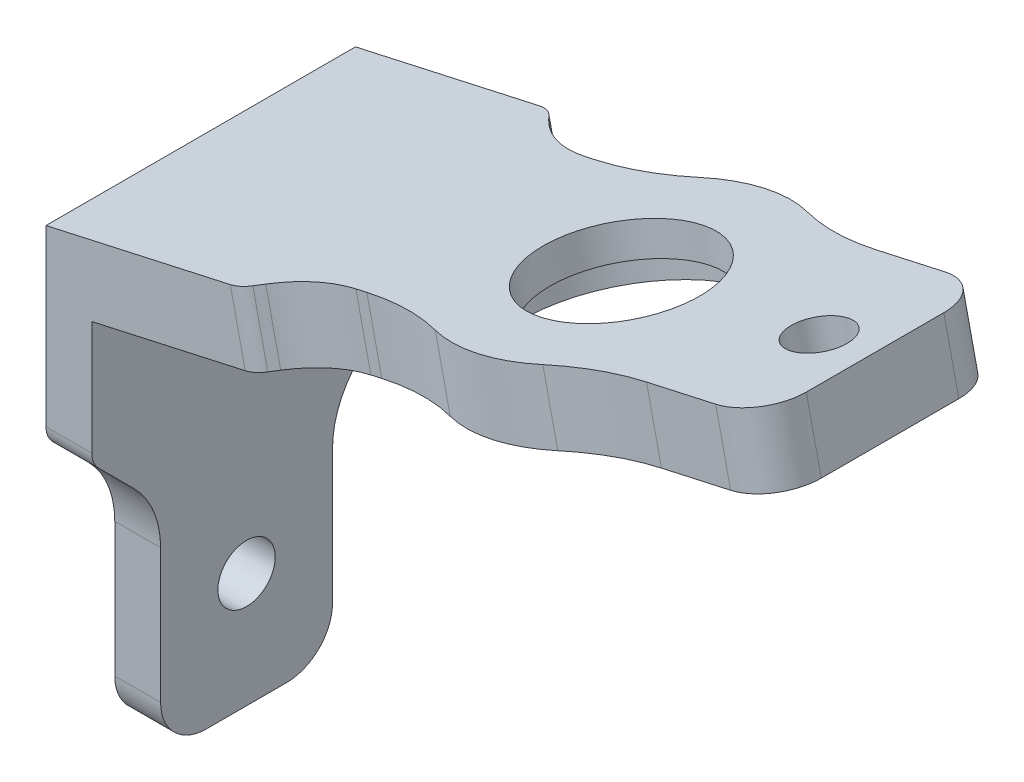
SolidWorks part; units mm, degrees
material "ABS"
ref_plane "Front Plane" through (0, 0, 0) normal (0, 0, 1) x (1, 0, 0)
ref_plane "Top Plane" through (0, 0, 0) normal (0, 1, 0) x (1, 0, 0)
ref_plane "Right Plane" through (0, 0, 0) normal (1, 0, 0) x (0, 0, -1)
sketch "Sketch2" plane through (-8.2998, 37.3265, 0) normal (-0.2171, 0.9762, 0) x (0.9762, 0.2171, 0)
  line L0 (-4.143, -6.75) -> (-4.143, 6.75) construction
  line L1 (-4.143, 6.75) -> (-8.9127, 6.75) construction
  line L2 (-8.9127, 6.75) -> (-8.9127, -6.75) construction
  line L3 (-8.9127, -6.75) -> (-4.143, -6.75) construction
  line L4 (-3.643, -6.75) -> (-2.0572, -6.75) construction
  line L5 (-1.3501, -6.4571) -> (-1.0646, -6.1716) construction
  line L6 (1.7639, -5) -> (14.3434, -5) construction
  line L7 (14.3434, -5) -> (14.3434, 5) construction
  line L8 (14.3434, 5) -> (1.7639, 5) construction
  line L9 (-1.0646, 6.1716) -> (-1.3501, 6.4571) construction
  line L10 (-2.0572, 6.75) -> (-3.643, 6.75) construction
  line L11 (-3.643, 6.75) -> (-3.643, -6.75) construction
  line L12 (19.8434, -3) -> (19.8434, 3) construction
  line L13 (17.8434, 5) -> (14.8434, 5) construction
  line L14 (14.8434, 5) -> (14.8434, -5) construction
  line L15 (14.8434, -5) -> (17.8434, -5) construction
  line L16 (-4.143, -6.75) -> (-4.143, 6.75) construction
  line L17 (-4.143, 6.75) -> (-8.9127, 6.75)
  line L18 (-8.9127, 6.75) -> (-8.9127, -6.75)
  line L19 (-8.9127, -6.75) -> (-4.143, -6.75)
  line L20 (-3.643, -6.75) -> (-2.0572, -6.75)
  line L21 (-1.3501, -6.4571) -> (-1.0646, -6.1716)
  line L22 (1.7639, -5) -> (14.3434, -5)
  line L23 (14.3434, -5) -> (14.3434, 5) construction
  line L24 (14.3434, 5) -> (1.7639, 5)
  line L25 (-1.0646, 6.1716) -> (-1.3501, 6.4571)
  line L26 (-2.0572, 6.75) -> (-3.643, 6.75)
  line L27 (-3.643, 6.75) -> (-3.643, -6.75) construction
  line L28 (19.8434, -3) -> (19.8434, 3)
  line L29 (17.8434, 5) -> (14.8434, 5)
  line L30 (14.8434, 5) -> (14.8434, -5) construction
  line L31 (14.8434, -5) -> (17.8434, -5)
  line L32 (-4.143, 6.75) -> (-3.643, 6.75)
  line L33 (-4.143, -6.75) -> (-3.643, -6.75)
  line L34 (14.3434, 5) -> (14.8434, 5)
  line L35 (14.3434, -5) -> (14.8434, -5)
  arc A0 (-2.0572, -6.75) -> (-1.3501, -6.4571) centre (-2.0572, -5.75) ccw construction
  arc A1 (1.7639, -5) -> (-1.0646, -6.1716) centre (1.7639, -9) ccw construction
  arc A2 (-1.0646, 6.1716) -> (1.7639, 5) centre (1.7639, 9) ccw construction
  arc A3 (-1.3501, 6.4571) -> (-2.0572, 6.75) centre (-2.0572, 5.75) ccw construction
  arc A4 (19.8434, 3) -> (17.8434, 5) centre (17.8434, 3) ccw construction
  arc A5 (17.8434, -5) -> (19.8434, -3) centre (17.8434, -3) ccw construction
  arc A6 (-2.0572, -6.75) -> (-1.3501, -6.4571) centre (-2.0572, -5.75) ccw
  arc A7 (1.7639, -5) -> (-1.0646, -6.1716) centre (1.7639, -9) ccw
  arc A8 (-1.0646, 6.1716) -> (1.7639, 5) centre (1.7639, 9) ccw
  arc A9 (-1.3501, 6.4571) -> (-2.0572, 6.75) centre (-2.0572, 5.75) ccw
  arc A10 (19.8434, 3) -> (17.8434, 5) centre (17.8434, 3) ccw
  arc A11 (17.8434, -5) -> (19.8434, -3) centre (17.8434, -3) ccw
extrude "Boss-Extrude1" add sketch "Sketch2" along normal blind 3
sketch "Sketch3" plane through (-17, 0, 0) normal (-1, 0, 0) x (0, 0, 1)
  line L0 (-6.75, 35.3919) -> (-6.75, 38.3204)
  line L1 (-6.75, 38.3204) -> (6.75, 38.3204)
  line L2 (6.75, 38.3204) -> (6.75, 35.3919)
  line L3 (-3.75, 20.3) -> (-3.75, 19.8)
  line L4 (-3.75, 19.8) -> (-3.75, 19.5)
  line L5 (-1.75, 17.5) -> (1.75, 17.5)
  line L6 (3.75, 19.5) -> (3.75, 19.8)
  line L7 (3.75, 19.8) -> (-3.75, 19.8)
  line L8 (-6.75, 35.3919) -> (-6.75, 30.4142)
  line L9 (-6.4571, 29.7071) -> (-4.9216, 28.1716)
  line L10 (-3.75, 25.3431) -> (-3.75, 20.3)
  line L11 (-3.75, 20.3) -> (3.75, 20.3)
  line L12 (3.75, 20.3) -> (3.75, 25.3431)
  line L13 (4.9216, 28.1716) -> (6.4571, 29.7071)
  line L14 (6.75, 30.4142) -> (6.75, 35.3919)
  line L15 (6.75, 35.3919) -> (-6.75, 35.3919)
  line L16 (-6.75, 35.3919) -> (-6.75, 30.4142)
  line L17 (-6.4571, 29.7071) -> (-4.9216, 28.1716)
  line L18 (-3.75, 25.3431) -> (-3.75, 20.3)
  line L19 (-3.75, 20.3) -> (3.75, 20.3) construction
  line L20 (3.75, 20.3) -> (3.75, 25.3431)
  line L21 (4.9216, 28.1716) -> (6.4571, 29.7071)
  line L22 (6.75, 30.4142) -> (6.75, 35.3919)
  line L23 (6.75, 35.3919) -> (-6.75, 35.3919) construction
  line L24 (-3.75, 19.8) -> (-3.75, 19.5)
  line L25 (-1.75, 17.5) -> (1.75, 17.5)
  line L26 (3.75, 19.5) -> (3.75, 19.8)
  line L27 (3.75, 19.8) -> (-3.75, 19.8) construction
  line L28 (3.75, 20.3) -> (3.75, 19.8)
  arc A2 (-3.75, 19.5) -> (-1.75, 17.5) centre (-1.75, 19.5) ccw
  arc A3 (1.75, 17.5) -> (3.75, 19.5) centre (1.75, 19.5) ccw
  arc A4 (-6.75, 30.4142) -> (-6.4571, 29.7071) centre (-5.75, 30.4142) ccw
  arc A5 (-3.75, 25.3431) -> (-4.9216, 28.1716) centre (-7.75, 25.3431) ccw
  arc A6 (4.9216, 28.1716) -> (3.75, 25.3431) centre (7.75, 25.3431) ccw
  arc A7 (6.4571, 29.7071) -> (6.75, 30.4142) centre (5.75, 30.4142) ccw
  arc A8 (-6.75, 30.4142) -> (-6.4571, 29.7071) centre (-5.75, 30.4142) ccw
  arc A9 (-3.75, 25.3431) -> (-4.9216, 28.1716) centre (-7.75, 25.3431) ccw
  arc A10 (4.9216, 28.1716) -> (3.75, 25.3431) centre (7.75, 25.3431) ccw
  arc A11 (6.4571, 29.7071) -> (6.75, 30.4142) centre (5.75, 30.4142) ccw
  arc A12 (-3.75, 19.5) -> (-1.75, 17.5) centre (-1.75, 19.5) ccw
  arc A13 (1.75, 17.5) -> (3.75, 19.5) centre (1.75, 19.5) ccw
  dimension "D1" = 0
  dimension "D2" = 0
extrude "Boss-Extrude2" add sketch "Sketch3" along normal blind 2
sketch "Sketch4" plane through (0, 0, 0) normal (0, 0, 1) x (1, 0, 0)
  line L0 (-17.6512, 38.3204) -> (-19, 38.0205)
  line L1 (-19, 30.4142) -> (-19, 38.3204) construction
  line L2 (-19, 38.0205) -> (-19, 38.3204)
  line L3 (-19, 38.3204) -> (-17.6512, 38.3204)
  line L4 (-17.6512, 38.3204) -> (-10.9591, 39.8084) construction
extrude "Cut-Extrude1" cut sketch "Sketch4" against normal through all both and the other way through all
sketch "Sketch5" plane through (-19, 0, 0) normal (-1, 0, 0) x (0, 0, 1)
  circle A0 centre (0, 22.5) radius 1.25 construction
  circle A1 centre (0, 22.5) radius 1.25
extrude "Cut-Extrude2" cut sketch "Sketch5" against normal through all
sketch "Sketch6" plane through (-8.9509, 40.2549, 0) normal (-0.2171, 0.9762, 0) x (0.9762, 0.2171, 0)
  circle A0 centre (17.3434, 0) radius 1.25 construction
  circle A1 centre (17.3434, 0) radius 1.25
extrude "Cut-Extrude3" cut sketch "Sketch6" against normal through all
sketch "Sketch7" plane through (-8.9509, 40.2549, 0) normal (-0.2171, 0.9762, 0) x (0.9762, 0.2171, 0)
  line L0 (5.4967, 0) -> (11.5083, 0) construction
  line L1 (5.4967, 0) -> (11.5083, 0) construction
  circle A0 centre (8.5025, 0) radius 3.5
  dimension "D1" = 7
extrude "Cut-Extrude4" cut sketch "Sketch7" against normal through all
sketch "Sketch8" plane through (-8.2998, 37.3265, 0) normal (0.2171, -0.9762, 0) x (0.9762, 0.2171, 0)
  circle A0 centre (8.5025, 0) radius 5.15
  dimension "D1" = 10.3
sketch "Sketch10" plane through (-8.9509, 40.2549, 0) normal (-0.2171, 0.9762, 0) x (0.9762, 0.2171, 0)
  circle A0 centre (8.5025, 0) radius 3.5
  circle A1 centre (8.5025, 0) radius 6.25
  circle A2 centre (8.5025, 0) radius 3.5 construction
  dimension "D1" = 12.5
extrude "Boss-Extrude3" add sketch "Sketch10" against normal up to surface (3 mm away) up to face at (-3.4166, 38.4123, 0)
extrude "Cut-Extrude5" cut sketch "Sketch8" against normal blind 1.6 contours A0
fillet "Fillet1" radius 10 2 edges at (-3.9862, 39.8222, -5) (3.335, 41.4502, 5)
